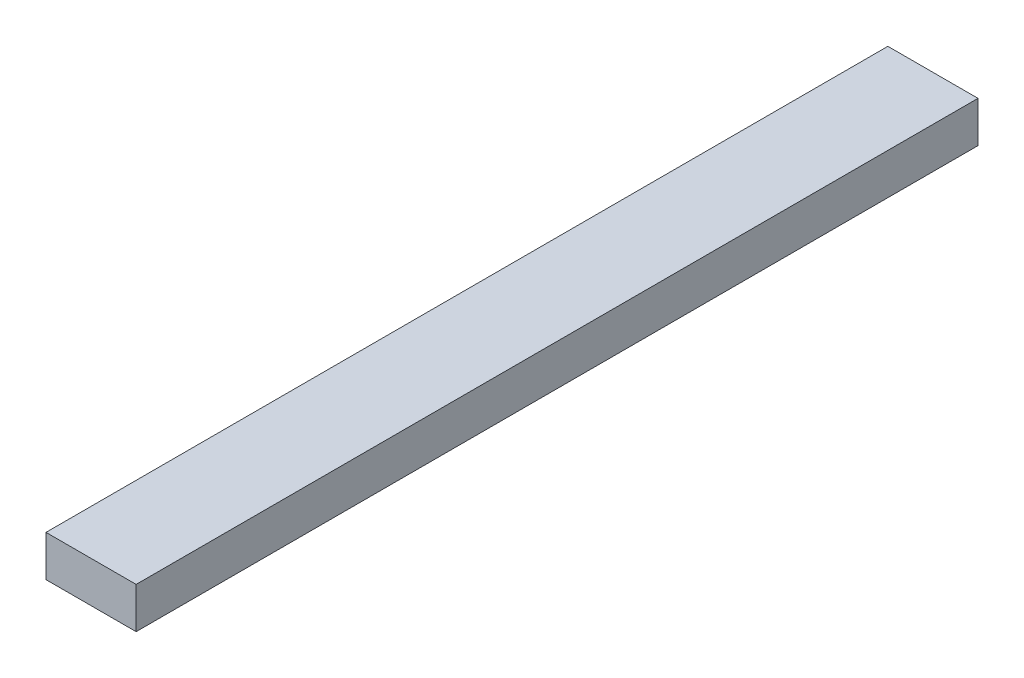
SolidWorks part; units mm, degrees
ref_plane "Front Plane" through (0, 0, 0) normal (0, 0, 1) x (1, 0, 0)
ref_plane "Top Plane" through (0, 0, 0) normal (0, 1, 0) x (1, 0, 0)
ref_plane "Right Plane" through (0, 0, 0) normal (1, 0, 0) x (0, 0, -1)
sketch "Sketch1" plane through (0, 0, 0) normal (0, 0, 1) x (1, 0, 0)
  line L1 (0, 0) -> (44, 0)
  line L2 (0, 0) -> (0, 20)
  line L3 (0, 20) -> (44, 20)
  line L4 (44, 0) -> (44, 20)
  dimension "D1" = 44
  dimension "D2" = 20
extrude "Boss-Extrude1" add sketch "Sketch1" against normal blind 411
